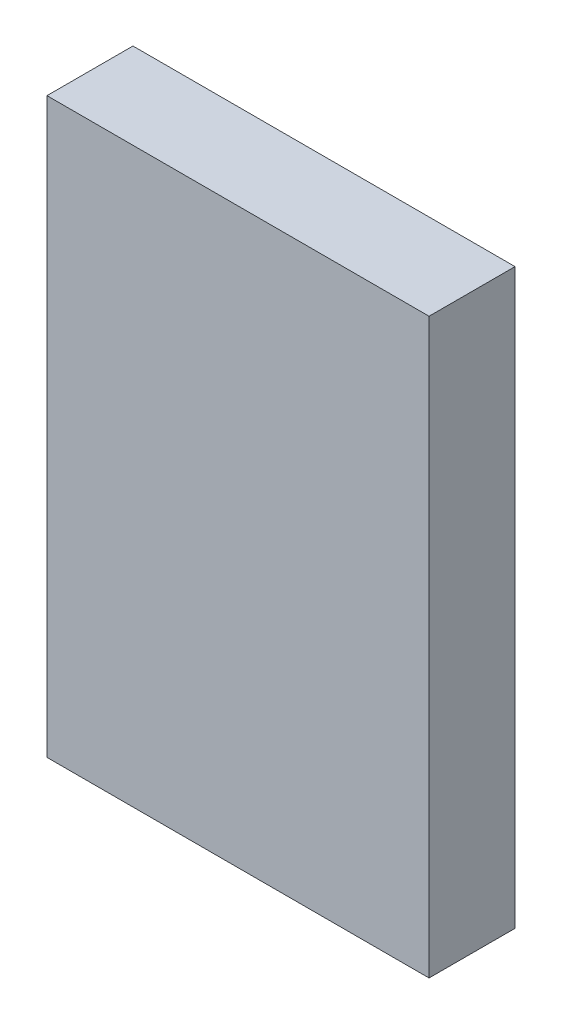
SolidWorks part; units mm, degrees
material "Balsa"
ref_plane "Front Plane" through (0, 0, 0) normal (0, 0, 1) x (1, 0, 0)
ref_plane "Top Plane" through (0, 0, 0) normal (0, 1, 0) x (1, 0, 0)
ref_plane "Right Plane" through (0, 0, 0) normal (1, 0, 0) x (0, 0, -1)
sketch "Sketch1" plane through (0, 0, 0) normal (0, 0, 1) x (1, 0, 0)
  line L1 (-40, 60) -> (40, 60)
  line L2 (-40, 60) -> (-40, -60)
  line L3 (-40, -60) -> (40, -60)
  line L4 (40, 60) -> (40, -60)
  line L5 (-40, 60) -> (40, -60) construction
  line L6 (-40, -60) -> (40, 60) construction
  point P0 (0, 0)
  dimension "D1" = 80
  dimension "D2" = 120
extrude "Boss-Extrude1" add sketch "Sketch1" along normal blind 18
